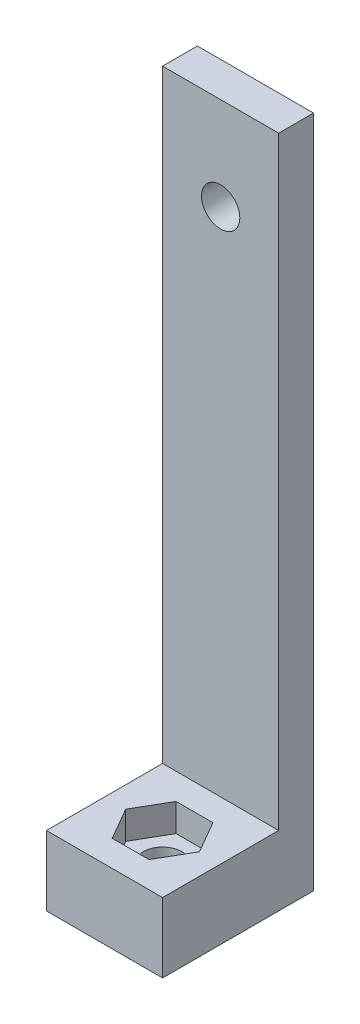
SolidWorks part; units mm, degrees
ref_plane "Front Plane" through (0, 0, 0) normal (0, 0, 1) x (1, 0, 0)
ref_plane "Top Plane" through (0, 0, 0) normal (0, 1, 0) x (1, 0, 0)
ref_plane "Right Plane" through (0, 0, 0) normal (1, 0, 0) x (0, 0, -1)
sketch "Sketch1" plane through (0, 0, 0) normal (0, 1, 0) x (1, 0, 0)
  line L0 (-5, -5) -> (5, -5)
  line L1 (5, -5) -> (5, 8)
  line L2 (5, 8) -> (-5, 8)
  line L3 (-5, 8) -> (-5, -5)
  circle A0 centre (0, 0) radius 1.65
  dimension "D1" = 3.3
  dimension "D2" = 10
  dimension "D3" = 5
  dimension "D4" = 5
  dimension "D5" = 13
extrude "Boss-Extrude1" add sketch "Sketch1" along normal blind 6
sketch "Sketch2" plane through (0, 6, 0) normal (0, 1, 0) x (1, 0, 0)
  line L1 (3.1754, 0) -> (1.5877, 2.75)
  line L2 (1.5877, 2.75) -> (-1.5877, 2.75)
  line L3 (-1.5877, 2.75) -> (-3.1754, 0)
  line L4 (-3.1754, 0) -> (-1.5877, -2.75)
  line L5 (-1.5877, -2.75) -> (1.5877, -2.75)
  line L6 (1.5877, -2.75) -> (3.1754, 0)
  circle A0 centre (0, 0) radius 2.75 construction
  dimension "D1" = 5.5
extrude "Cut-Extrude1" cut sketch "Sketch2" against normal blind 2.4
sketch "Sketch3" plane through (0, 0, -8) normal (0, 0, -1) x (-1, 0, 0)
  line L1 (-5, 0) -> (5, 0)
  line L2 (-5, 0) -> (-5, 58)
  line L3 (-5, 58) -> (5, 58)
  line L4 (5, 0) -> (5, 58)
  dimension "D1" = 58
  dimension "D2" = 10
extrude "Boss-Extrude2" add sketch "Sketch3" against normal blind 3
sketch "Sketch4" plane through (0, 0, -5) normal (0, 0, 1) x (1, 0, 0)
  line L1 (-5, 58) -> (5, 58) construction
  circle A1 centre (0, 50) radius 1.65
  dimension "D1" = 3.3
  dimension "D2" = 8
extrude "Cut-Extrude2" cut sketch "Sketch4" against normal blind 3
